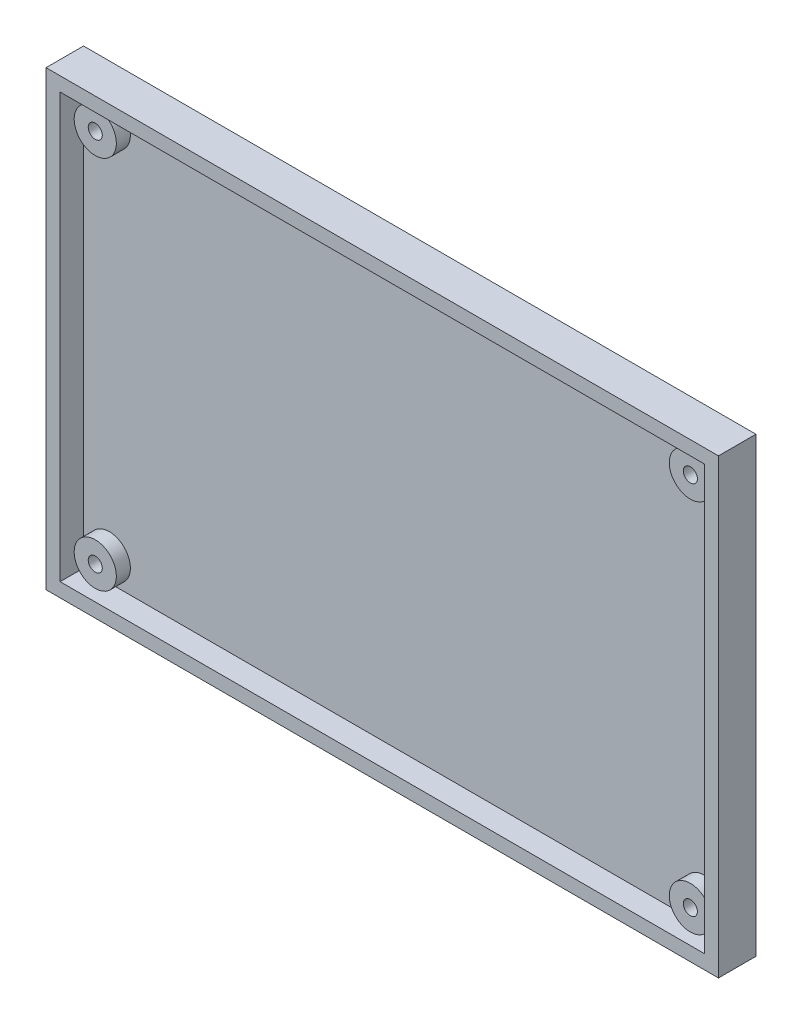
SolidWorks part; units mm, degrees
ref_plane "Front Plane" through (0, 0, 0) normal (0, 0, 1) x (1, 0, 0)
ref_plane "Top Plane" through (0, 0, 0) normal (0, 1, 0) x (1, 0, 0)
ref_plane "Right Plane" through (0, 0, 0) normal (1, 0, 0) x (0, 0, -1)
sketch "Sketch1" plane through (0, 0, 0) normal (0, 0, 1) x (1, 0, 0)
  line L1 (0, 0) -> (143.5, 0)
  line L2 (0, 0) -> (0, 96.5)
  line L3 (0, 96.5) -> (143.5, 96.5)
  line L4 (143.5, 0) -> (143.5, 96.5)
  circle A0 centre (8.5, 88) radius 1.5
  circle A1 centre (8.5, 8) radius 1.5
  circle A2 centre (135.5, 8) radius 1.5
  circle A3 centre (135.5, 88) radius 1.5
  dimension "D7" = 3
  dimension "D1" = 96.5
  dimension "D2" = 143.5
  dimension "D3" = 8.5
  dimension "D4" = 8.5
  dimension "D5" = 8
  dimension "D6" = 8
extrude "Boss-Extrude1" add sketch "Sketch1" along normal blind 8
shell "Shell1" thickness 3
sketch "Sketch2" plane through (0, 0, 8) normal (0, 0, 1) x (1, 0, 0)
  line L1 (3, 3) -> (140.5, 3)
  line L2 (3, 3) -> (3, 93.5)
  line L3 (3, 93.5) -> (140.5, 93.5)
  line L4 (140.5, 3) -> (140.5, 93.5)
extrude "Cut-Extrude1" cut sketch "Sketch2" against normal blind 2
